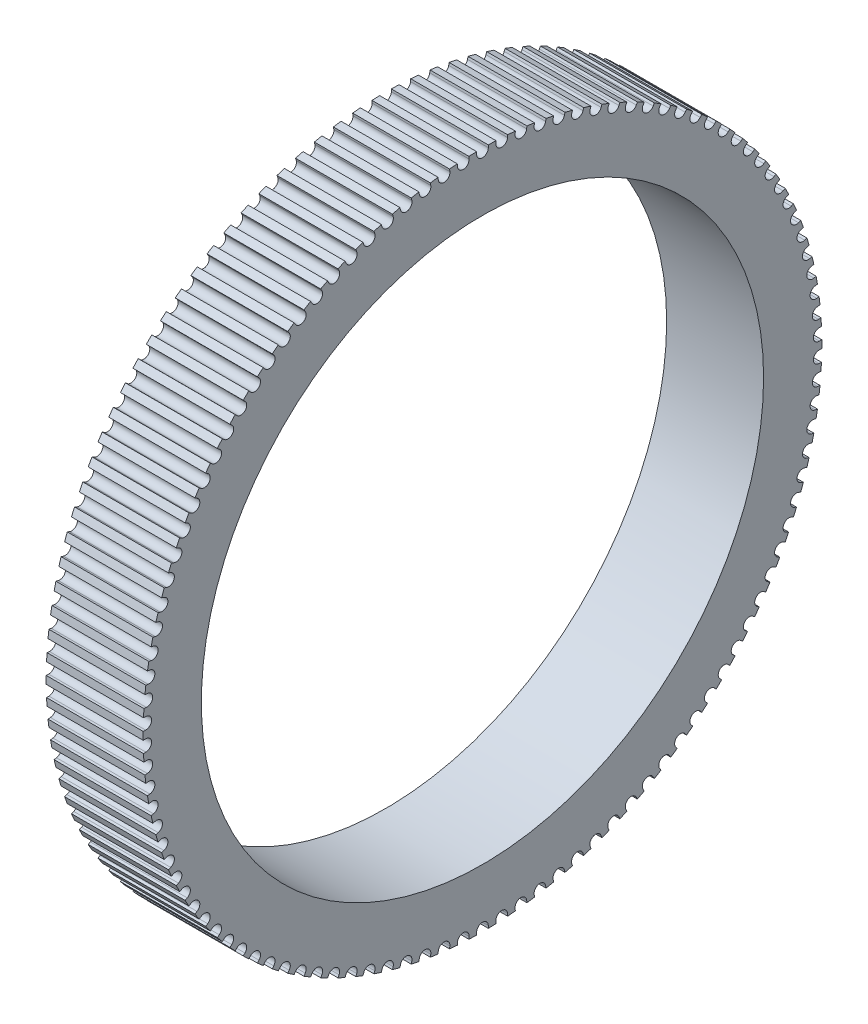
SolidWorks part; units mm, degrees
material "PA Type 6"
ref_plane "Front Plane" through (0, 0, 0) normal (0, 0, 1) x (1, 0, 0)
ref_plane "Top Plane" through (0, 0, 0) normal (0, 1, 0) x (1, 0, 0)
ref_plane "Right Plane" through (0, 0, 0) normal (1, 0, 0) x (0, 0, -1)
sketch "Sketch1" plane through (0, 0, 0) normal (1, 0, 0) x (0, 0, -1)
  circle A0 centre (0, 0) radius 29
  circle A1 centre (0, 0) radius 35
extrude "Boss-Extrude1" add sketch "Sketch1" along normal blind 10
sketch "Sketch2" plane through (10, 0, 0) normal (1, 0, 0) x (0, 0, -1)
  line L0 (0, 36.5003) -> (0, 34.747) construction
  line L1 (0.6, 36.5003) -> (0.6, 34.747)
  line L2 (-0.6, 36.5003) -> (-0.6, 34.747)
  arc A0 (0.6, 36.5003) -> (-0.6, 36.5003) centre (0, 36.5003) ccw
  arc A1 (-0.6, 34.747) -> (0.6, 34.747) centre (0, 34.747) ccw
  point P3 (0, 35.6237)
  point P8 (0, 34.747)
  dimension "D1" = 0.6
extrude "Cut-Extrude1" cut sketch "Sketch2" against normal blind 10
pattern_circular "CirPattern1" count 110 over 360 about axis through (0, 0, 0) along (1, 0, 0) of "Cut-Extrude1"
